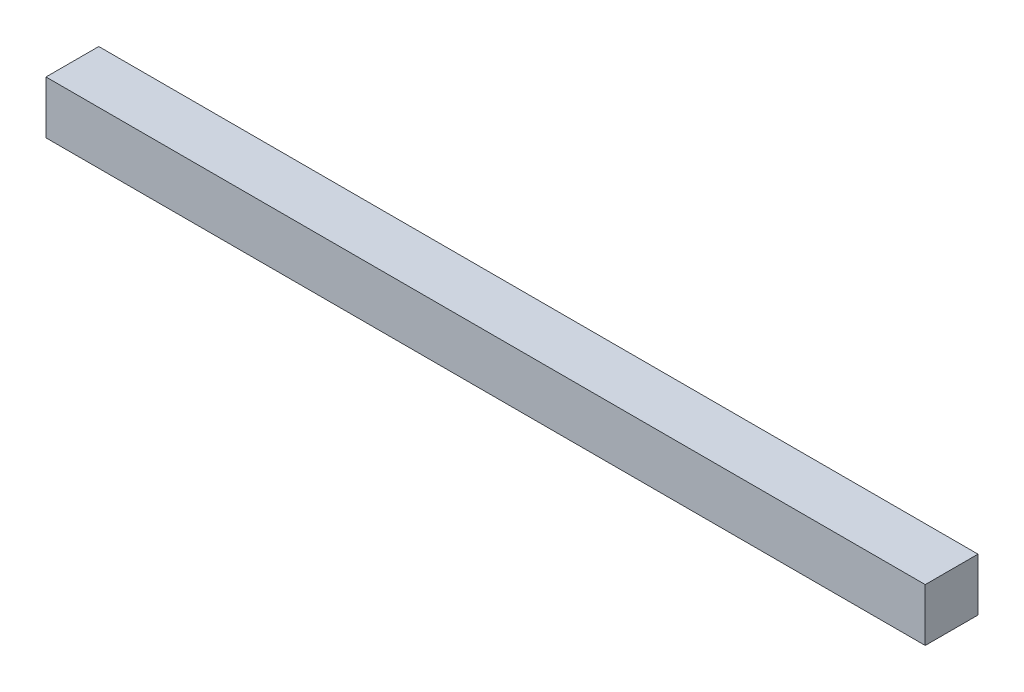
SolidWorks part; units mm, degrees
ref_plane "정면" through (0, 0, 0) normal (0, 0, 1) x (1, 0, 0)
ref_plane "윗면" through (0, 0, 0) normal (0, 1, 0) x (1, 0, 0)
ref_plane "우측면" through (0, 0, 0) normal (1, 0, 0) x (0, 0, -1)
sketch "스케치1" plane through (0, 0, 0) normal (1, 0, 0) x (0, 0, -1)
  line L1 (-15, -15) -> (15, -15)
  line L2 (-15, -15) -> (-15, 15)
  line L3 (-15, 15) -> (15, 15)
  line L4 (15, -15) -> (15, 15)
  line L5 (-15, -15) -> (15, 15) construction
  line L6 (-15, 15) -> (15, -15) construction
  point P0 (0, 0)
  dimension "D1" = 30
  dimension "D2" = 30
extrude "보스-돌출1" add sketch "스케치1" along normal blind 500
